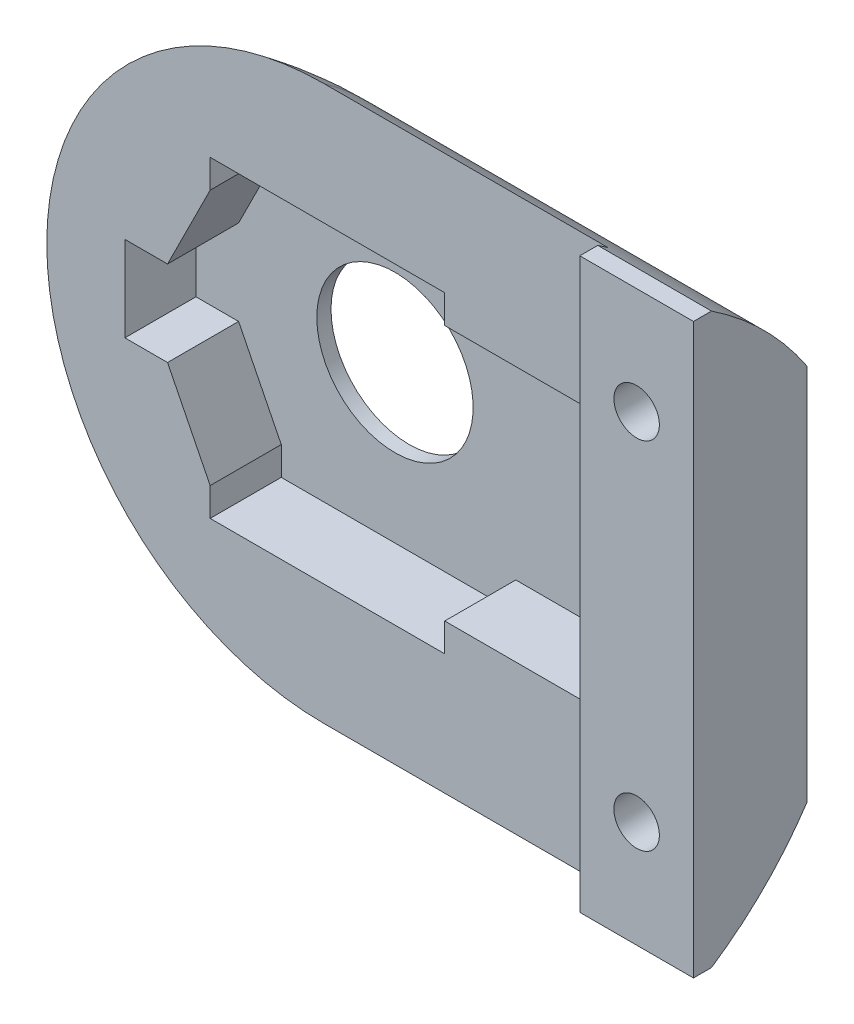
SolidWorks part; units mm, degrees
ref_plane "Front Plane" through (0, 0, 0) normal (0, 0, 1) x (1, 0, 0)
ref_plane "Top Plane" through (0, 0, 0) normal (0, 1, 0) x (1, 0, 0)
ref_plane "Right Plane" through (0, 0, 0) normal (1, 0, 0) x (0, 0, -1)
sketch "Sketch1" plane through (0, 0, 0) normal (0, 0, 1) x (1, 0, 0)
  line L0 (0, 10) -> (14, 10)
  line L1 (14, 10) -> (14, -10)
  line L2 (14, -10) -> (0, -10)
  circle A0 centre (0, 0) radius 10
extrude "Boss-Extrude1" add sketch "Sketch1" along normal blind 4 contours A0 | A0 L2 L1 L0
sketch "Sketch2" plane through (0, 0, 0) normal (0, 0, 1) x (1, 0, 0)
  line L0 (0, 10) -> (10, 10)
  line L1 (0, 10) -> (14, 10) construction
  line L2 (10, 10) -> (10, 0)
  line L3 (10, 0) -> (10, -10)
  line L4 (14, -10) -> (0, -10) construction
  line L5 (10, -10) -> (0, -10)
  circle A0 centre (0, 0) radius 10
extrude "Body Hole" cut sketch "Sketch2" against normal blind 2 from offset 5 contours A0 | A0 L2 L0 | A0 L5 L3
sketch "Sketch5" plane through (0, 0, 0) normal (0, 0, 1) x (1, 0, 0)
  line L0 (10, 0) -> (12, 0) construction
  line L1 (12, 0) -> (12, 6.25) construction
  line L2 (12, 0) -> (12, -6.25) construction
  circle A1 centre (12, 6.25) radius 0.8
  circle A2 centre (12, -6.25) radius 0.8
extrude "Screw Holes" cut sketch "Sketch5" along normal through all
sketch "Sketch6" plane through (0, 0, 0) normal (0, 0, 1) x (1, 0, 0)
  circle A1 centre (12, -6.25) radius 1.25
extrude "Screw Heads" cut sketch "Sketch6" along normal blind 2
sketch "Sketch3" plane through (28.2876, 0, 0) normal (0, 0, 1) x (1, 0, 0)
  line L26 (-28.2876, 0) -> (-35.2876, 0) construction
  line L27 (-28.2876, 0) -> (-18.7876, 0) construction
  line L28 (-28.2876, 0) -> (-28.2876, 5.5) construction
  line L29 (-28.2876, 0) -> (-28.2876, -5.5) construction
  line L30 (-35.2876, 0) -> (-35.2876, -1.5)
  line L31 (-35.2876, -1.5) -> (-33.7876, -1.5)
  line L32 (-33.7876, -1.5) -> (-32.2876, -1.5) construction
  line L33 (-32.2876, -1.5) -> (-32.2876, -4.5) construction
  line L34 (-33.7876, -1.5) -> (-32.2876, -4.5)
  line L35 (-32.2876, -4.5) -> (-32.2876, -5.5)
  line L36 (-32.2876, -5.5) -> (-28.2876, -5.5)
  line L37 (-28.2876, -5.5) -> (-24.0376, -5.5)
  line L38 (-24.0376, -5.5) -> (-24.0376, -4.5)
  line L39 (-24.0376, -4.5) -> (-18.7876, -4.5)
  line L40 (-18.7876, -4.5) -> (-18.7876, 0)
  line L41 (-35.2876, 0) -> (-35.2876, 1.5)
  line L42 (-35.2876, 1.5) -> (-33.7876, 1.5)
  line L43 (-33.7876, 1.5) -> (-32.2876, 1.5) construction
  line L44 (-32.2876, 1.5) -> (-32.2876, 4.5) construction
  line L45 (-33.7876, 1.5) -> (-32.2876, 4.5)
  line L46 (-32.2876, 4.5) -> (-32.2876, 5.5)
  line L47 (-32.2876, 5.5) -> (-28.2876, 5.5)
  line L48 (-28.2876, 5.5) -> (-24.0376, 5.5)
  line L49 (-24.0376, 5.5) -> (-24.0376, 4.5)
  line L50 (-24.0376, 4.5) -> (-18.7876, 4.5)
  line L51 (-18.7876, 4.5) -> (-18.7876, 0)
extrude "Pot Insert" cut sketch "Sketch3" along normal blind 2.5 from offset 0.5
sketch "Sketch4" plane through (0, 0, 0) normal (0, 0, 1) x (1, 0, 0)
  circle A0 centre (0, 0) radius 2.75
extrude "Pot Hole" cut sketch "Sketch4" along normal through all
sketch "Sketch11" plane through (0, 0, 0) normal (1, 0, 0) x (0, 0, -1)
  line L0 (0, 0) -> (-10, 0) construction
  line L1 (-10, 0) -> (2, 0) construction
  line L2 (2, 0) -> (2, 12)
  line L3 (2, 12) -> (-10, 12)
  line L4 (2, 0) -> (2, 2.75) construction
  line L5 (2, 2.75) -> (1.6806, 2.75)
  arc A0 (2, 0) -> (-10, 12) centre (-10, 0) ccw
revolve "Cut-Revolve6" cut sketch "Sketch11" angle 180 about L0
sketch "Sketch13" plane through (0, 0, 0) normal (1, 0, 0) x (0, 0, -1)
  line L0 (0, 0) -> (-10, 0) construction
  line L1 (-10, 0) -> (2, 0) construction
  line L2 (2, 0) -> (2, 12)
  line L3 (2, 12) -> (-10, 12)
  line L4 (2, 0) -> (2, -12)
  line L5 (2, -12) -> (-10, -12)
  arc A0 (-10, 12) -> (2, 0) centre (-10, 0) cw
  arc A1 (2, 0) -> (-10, -12) centre (-10, 0) cw
extrude "Cut-Extrude1" cut sketch "Sketch13" along normal through all contours L3 A0 L2 | L4 A1 L5
